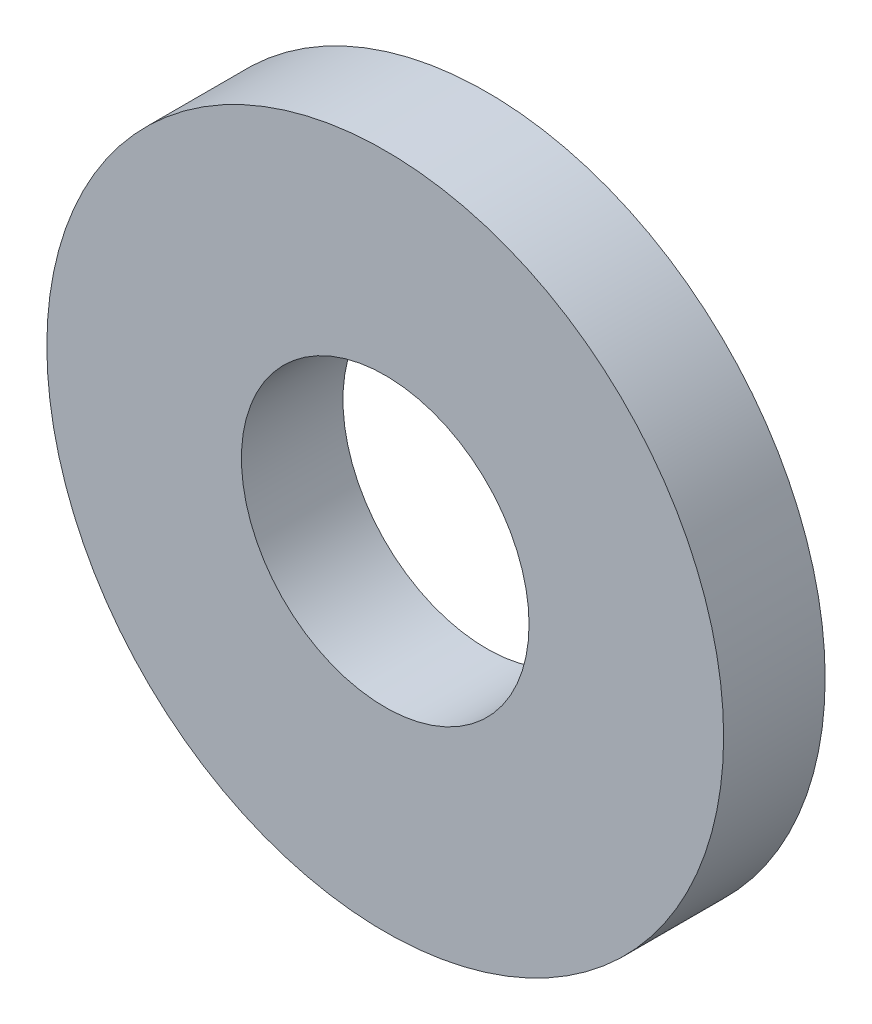
SolidWorks part; units mm, degrees
ref_plane "Front Plane" through (0, 0, 0) normal (0, 0, 1) x (1, 0, 0)
ref_plane "Top Plane" through (0, 0, 0) normal (0, 1, 0) x (1, 0, 0)
ref_plane "Right Plane" through (0, 0, 0) normal (1, 0, 0) x (0, 0, -1)
sketch "Sketch1" plane through (0, 0, 0) normal (0, 0, 1) x (1, 0, 0)
  circle A0 centre (350, 60) radius 8.5
  circle A1 centre (350, 60) radius 20
  dimension "D1" = 40
  dimension "D2" = 17
extrude "Boss-Extrude1" add sketch "Sketch1" along normal blind 6
